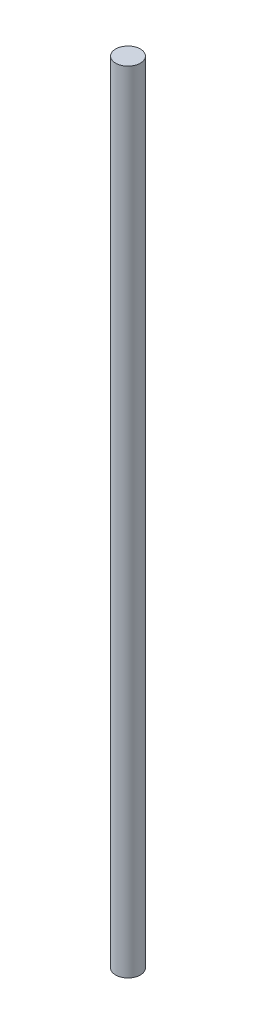
SolidWorks part; units mm, degrees
ref_plane "Front Plane" through (0, 0, 0) normal (0, 0, 1) x (1, 0, 0)
ref_plane "Top Plane" through (0, 0, 0) normal (0, 1, 0) x (1, 0, 0)
ref_plane "Right Plane" through (0, 0, 0) normal (1, 0, 0) x (0, 0, -1)
sketch "Sketch1" plane through (0, 0, 0) normal (0, 1, 0) x (1, 0, 0)
  circle A0 centre (0, 0) radius 1.5875
  dimension "D1" = 3.175
extrude "Boss-Extrude1" add sketch "Sketch1" along normal blind 101.6
